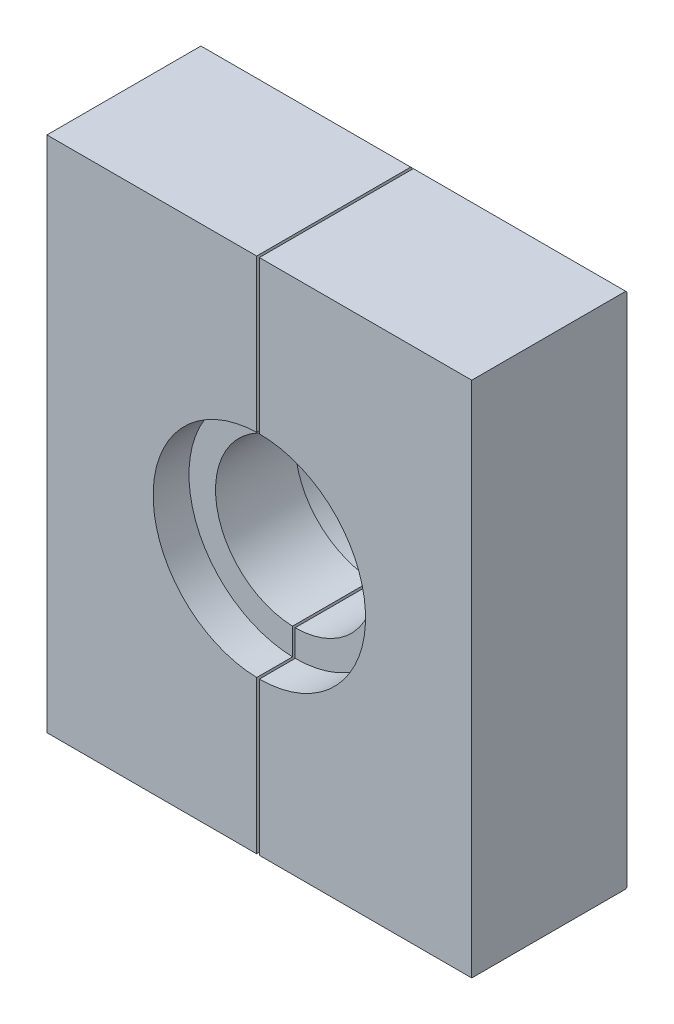
SolidWorks part; units mm, degrees
ref_plane "Přední rovina" through (0, 0, 0) normal (0, 0, 1) x (1, 0, 0)
ref_plane "Horní rovina" through (0, 0, 0) normal (0, 1, 0) x (1, 0, 0)
ref_plane "Pravá rovina" through (0, 0, 0) normal (1, 0, 0) x (0, 0, -1)
sketch "Skica1" plane through (0, 0, 0) normal (0, 0, 1) x (1, 0, 0)
  line L1 (-18.0816, -27) -> (-18.0816, 12)
  line L2 (-18.0816, 12) -> (13.9184, 12)
  line L3 (13.9184, 12) -> (13.9184, -27)
  line L4 (13.9184, -27) -> (-18.0816, -27)
  circle A0 centre (-2.0816, -7.5) radius 6
  circle A1 centre (-2.0816, -7.5) radius 8
  point P3 (-2.0816, -4.7564)
  dimension "D6" = 12
  dimension "D1" = 19.5
  dimension "D2" = 32
  dimension "D3" = 39
  dimension "D4" = 16
extrude "Přidat vysunutím1" add sketch "Skica1" along normal blind 12.7 contours L4 L3 L2 L1 A1 | A1 A0
sketch "Skica3" plane through (0, 0, 12.7) normal (0, 0, 1) x (1, 0, 0)
  circle A0 centre (-2.0816, -7.5) radius 8
extrude "Odebrat vysunutím2" cut sketch "Skica3" against normal blind 3.7
sketch "Skica4" plane through (0, 0, 0) normal (0, 0, -1) x (-1, 0, 0)
  circle A0 centre (2.0816, -7.5) radius 8
extrude "Odebrat vysunutím3" cut sketch "Skica4" against normal blind 3
chamfer "Zkosení1" distance 0.1 angle 45 8 edges at (-2.0816, -27, 0) (-2.0816, -27, 12.7) (-2.0816, 12, 12.7) (-2.0816, 12, 0) (13.9184, -27, 6.35) (13.9184, -7.5, 12.7) (13.9184, 12, 6.35) (13.9184, -7.5, 0)
sketch "Skica10" plane through (0, 0, 12.7) normal (0, 0, 1) x (1, 0, 0)
  line L8 (-2.0816, 12) -> (-2.0816, -27)
  line L9 (-18.0816, 12) -> (13.9184, 12) construction
  line L10 (13.9184, -27) -> (-18.0816, -27) construction
  line L11 (-2.0816, -27) -> (-2.2816, -27)
  line L12 (-2.2816, -27) -> (-2.2816, 12)
  line L13 (-2.2816, 12) -> (-2.0816, 12)
  dimension "D1" = 0.2
extrude "Odebrat vysunutím13" cut sketch "Skica10" against normal up to vertex
sketch "Sketch1" plane through (0, 0, 12.7) normal (0, 0, 1) x (1, 0, 0)
  line L1 (-30.6863, 14.5708) -> (27.8241, 14.5708)
  line L2 (-30.6863, 14.5708) -> (-30.6863, -30.5357)
  line L3 (-30.6863, -30.5357) -> (27.8241, -30.5357)
  line L4 (27.8241, 14.5708) -> (27.8241, -30.5357)
  point P4 (27.8241, -30.5357)
extrude "Cut-Extrude1" cut sketch "Sketch1" against normal blind 1
